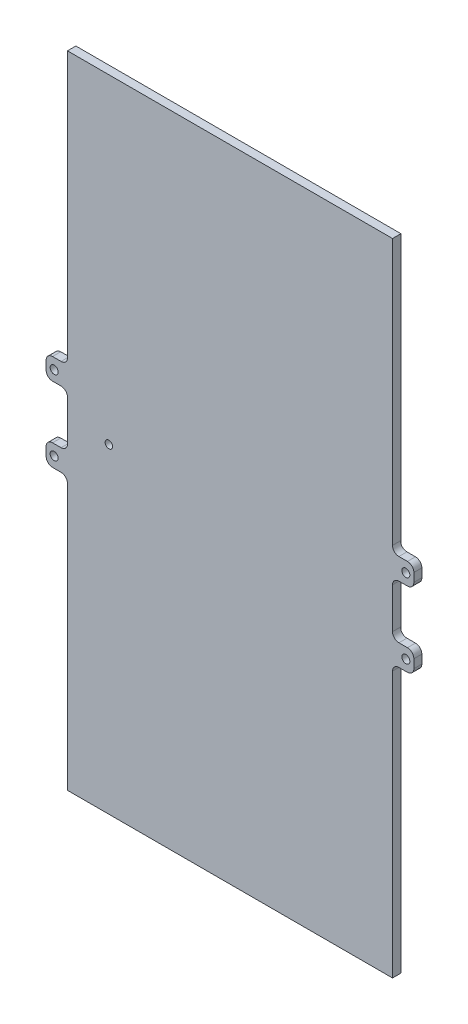
SolidWorks part; units mm, degrees
ref_plane "Front Plane" through (0, 0, 0) normal (1, 0, 0) x (0, 1, 0)
ref_plane "Top Plane" through (0, 0, 0) normal (0, 0, 1) x (0, 1, 0)
ref_plane "Right Plane" through (0, 0, 0) normal (0, 1, 0) x (-1, 0, 0)
sketch "Sketch1" plane through (0, 0, 0) normal (0, 0, 1) x (0, 1, 0)
  line L1 (-60, -30.45) -> (60, -30.45)
  line L2 (-60, -30.45) -> (-60, 30.45)
  line L3 (-60, 30.45) -> (60, 30.45)
  line L4 (60, -30.45) -> (60, 30.45)
  line L5 (-60, -30.45) -> (60, 30.45) construction
  line L6 (-60, 30.45) -> (60, -30.45) construction
  point P0 (0, 0)
  dimension "D1" = 120
  dimension "D2" = 60.9
extrude "Boss-Extrude1" add sketch "Sketch1" along normal blind 1.61
sketch "Sketch2" plane through (0, 0, 0) normal (0, 0, -1) x (1, 0, 0)
  line L1 (28.4817, 0) -> (17.4151, 6.3893)
  line L2 (17.4151, 6.3893) -> (17.4151, -6.3893)
  line L3 (17.4151, -6.3893) -> (28.4817, 0)
  circle A0 centre (21.104, 0) radius 3.6889 construction
extrude "Cut-Extrude1" cut sketch "Sketch2" against normal blind 0.5 contours L3 L1 L2
sketch "Sketch3" plane through (-30.45, 0, 0) normal (-1, 0, 0) x (0, -1, 0)
  line L0 (-60, 1.61) -> (-60, 0) construction
  line L1 (60, 0.035) -> (-60, 0.035)
  line L2 (60, 0.035) -> (60, 1.575)
  line L3 (60, 1.575) -> (-60, 1.575)
  line L4 (-60, 0.035) -> (-60, 1.575)
  line L5 (60, 0.035) -> (-60, 1.575) construction
  line L6 (60, 1.575) -> (-60, 0.035) construction
  line L7 (-60, 1.61) -> (60, 1.61) construction
  line L8 (-60, 0) -> (60, 0) construction
  line L9 (-9, 0.035) -> (-5, 0.035)
  line L10 (-9, 0.035) -> (-9, 1.575)
  line L11 (-9, 1.575) -> (-5, 1.575)
  line L12 (-5, 0.035) -> (-5, 1.575)
  line L13 (-9, 0.035) -> (-5, 1.575) construction
  line L14 (-9, 1.575) -> (-5, 0.035) construction
  line L15 (5, 0.035) -> (9, 0.035)
  line L16 (5, 0.035) -> (5, 1.575)
  line L17 (5, 1.575) -> (9, 1.575)
  line L18 (9, 0.035) -> (9, 1.575)
  line L19 (5, 0.035) -> (9, 1.575) construction
  line L20 (5, 1.575) -> (9, 0.035) construction
  point P0 (0, 0.805)
  point P9 (-7, 0.805)
  point P14 (7, 0.805)
  dimension "D1" = 0.035
  dimension "D2" = 0.035
  dimension "D3" = 4
  dimension "D4" = 4
  dimension "D5" = 5
  dimension "D6" = 5
sketch "Sketch5" plane through (30.45, 0, 0) normal (1, 0, 0) x (0, 1, 0)
  line L0 (-60, 0.035) -> (-60, 1.575) construction
  line L1 (60, 1.54) -> (-60, 1.54)
  line L2 (60, 1.54) -> (60, 0.07)
  line L3 (60, 0.07) -> (-60, 0.07)
  line L4 (-60, 1.54) -> (-60, 0.07)
  line L5 (60, 1.54) -> (-60, 0.07) construction
  line L6 (60, 0.07) -> (-60, 1.54) construction
  line L7 (-60, 0.035) -> (60, 0.035) construction
  line L9 (9, 0.07) -> (5, 0.07)
  line L10 (9, 0.07) -> (9, 1.54)
  line L11 (9, 1.54) -> (5, 1.54)
  line L12 (5, 0.07) -> (5, 1.54)
  line L13 (9, 0.07) -> (5, 1.54) construction
  line L14 (9, 1.54) -> (5, 0.07) construction
  line L15 (-9, 0.07) -> (-5, 0.07)
  line L16 (-9, 0.07) -> (-9, 1.54)
  line L17 (-9, 1.54) -> (-5, 1.54)
  line L18 (-5, 0.07) -> (-5, 1.54)
  line L19 (-9, 0.07) -> (-5, 1.54) construction
  line L20 (-9, 1.54) -> (-5, 0.07) construction
  point P0 (0, 0.805)
  point P10 (7, 0.805)
  point P15 (-7, 0.805)
  dimension "D1" = 0.035
  dimension "D2" = 4
  dimension "D3" = 4
  dimension "D4" = 5
  dimension "D5" = 5
extrude "Boss-Extrude2" add sketch "Sketch3" along normal blind 4 contours L10 L11 L12 L9 | L18 L17 L16 L15
extrude "Boss-Extrude3" add sketch "Sketch5" along normal blind 4 contours L12 L11 L10 L9 | L18 L17 L16 L15
sketch "Sketch7" plane through (0, 0, 1.54) normal (0, 0, 1) x (1, 0, 0)
  line L0 (-34.45, 9) -> (-30.45, 9) construction
  line L1 (-34.45, 9) -> (-34.45, 5) construction
  line L2 (-34.45, -9) -> (-30.45, -9) construction
  line L3 (-34.45, -5) -> (-34.45, -9) construction
  line L4 (34.45, -9) -> (30.45, -9) construction
  line L5 (34.45, -9) -> (34.45, -5) construction
  line L6 (34.45, 9) -> (30.45, 9) construction
  line L7 (34.45, 9) -> (34.45, 5) construction
  circle A0 centre (32.95, 7) radius 0.75
  circle A1 centre (32.95, -7) radius 0.75
  circle A2 centre (-32.95, -7) radius 0.75
  circle A3 centre (-32.95, 7) radius 0.75
  dimension "D1" = 1.5
  dimension "D2" = 1.5
  dimension "D3" = 1.5
  dimension "D4" = 1.5
  dimension "D8" = 1.5
  dimension "D9" = 2
  dimension "D10" = 1.5
  dimension "D11" = 2
  dimension "D12" = 1.5
  dimension "D5" = 2
  dimension "D6" = 1.5
  dimension "D7" = 2
extrude "Cut-Extrude3" cut sketch "Sketch7" against normal through all both and the other way through all contours A0 | A1 | A2 | A3
fillet "Fillet1" radius 1.2 8 edges at (30.45, 9, 0.805) (30.45, -5, 0.805) (30.45, -9, 0.805) (30.45, 5, 0.805) (-30.45, 9, 0.805) (-30.45, 5, 0.805) (-30.45, -9, 0.805) (-30.45, -5, 0.805)
fillet "Fillet2" radius 1.2 8 edges at (-34.45, -9, 0.805) (-34.45, -5, 0.805) (-34.45, 5, 0.805) (-34.45, 9, 0.805) (34.45, 9, 0.805) (34.45, 5, 0.805) (34.45, -9, 0.805) (34.45, -5, 0.805)
sketch "Sketch8" plane through (0, 0, 0) normal (0, 0, -1) x (1, 0, 0)
  line L0 (-30.45, -60) -> (-30.45, 60) construction
  circle A0 centre (-22.7, 0) radius 0.7
  dimension "D2" = 1.4
  dimension "D1" = 7.75
extrude "Cut-Extrude4" cut sketch "Sketch8" against normal through all contours A0
sketch "Sketch9" plane through (0, 0, 0.07) normal (0, 0, -1) x (-1, 0, 0)
  line L0 (-30.45, -10.2) -> (-30.45, -3.8) construction
  point P0 (-30.45, -7)
sketch "Sketch13" plane through (0, 0, 1.61) normal (0, 0, 1) x (1, 0, 0)
  line L1 (-30.45, 60) -> (30.45, 60)
  line L2 (-30.45, 60) -> (-30.45, -60)
  line L3 (-30.45, -60) -> (30.45, -60)
  line L4 (30.45, 60) -> (30.45, -60)
extrude "Cut-Extrude5" cut sketch "Sketch13" against normal blind 0.04
sketch "Sketch14" plane through (0, 0, 1.54) normal (0, 0, 1) x (1, 0, 0)
  line L0 (31.65, -9) -> (33.25, -9) construction
  line L1 (34.45, -7.8) -> (34.45, -6.2) construction
  line L2 (33.25, -5) -> (31.65, -5) construction
  line L3 (30.45, -3.8) -> (30.45, -10.2) construction
  line L4 (34.45, 6.2) -> (34.45, 7.8) construction
  line L5 (33.25, 9) -> (31.65, 9) construction
  line L6 (30.45, 10.2) -> (30.45, 3.8) construction
  line L7 (31.65, 5) -> (33.25, 5) construction
  line L8 (31.65, -9) -> (33.25, -9)
  line L9 (34.45, -7.8) -> (34.45, -6.2)
  line L10 (33.25, -5) -> (31.65, -5)
  line L11 (30.45, -3.8) -> (30.45, -10.2)
  line L12 (34.45, 6.2) -> (34.45, 7.8)
  line L13 (33.25, 9) -> (31.65, 9)
  line L14 (30.45, 10.2) -> (30.45, 3.8)
  line L15 (31.65, 5) -> (33.25, 5)
  arc A0 (33.25, -9) -> (34.45, -7.8) centre (33.25, -7.8) ccw construction
  arc A1 (34.45, -6.2) -> (33.25, -5) centre (33.25, -6.2) ccw construction
  arc A2 (30.45, -3.8) -> (31.65, -5) centre (31.65, -3.8) ccw construction
  arc A3 (31.65, -9) -> (30.45, -10.2) centre (31.65, -10.2) ccw construction
  arc A4 (34.45, 7.8) -> (33.25, 9) centre (33.25, 7.8) ccw construction
  arc A5 (30.45, 10.2) -> (31.65, 9) centre (31.65, 10.2) ccw construction
  arc A6 (31.65, 5) -> (30.45, 3.8) centre (31.65, 3.8) ccw construction
  arc A7 (33.25, 5) -> (34.45, 6.2) centre (33.25, 6.2) ccw construction
  arc A8 (33.25, -9) -> (34.45, -7.8) centre (33.25, -7.8) ccw
  arc A9 (34.45, -6.2) -> (33.25, -5) centre (33.25, -6.2) ccw
  arc A10 (30.45, -3.8) -> (31.65, -5) centre (31.65, -3.8) ccw
  arc A11 (31.65, -9) -> (30.45, -10.2) centre (31.65, -10.2) ccw
  arc A12 (34.45, 7.8) -> (33.25, 9) centre (33.25, 7.8) ccw
  arc A13 (30.45, 10.2) -> (31.65, 9) centre (31.65, 10.2) ccw
  arc A14 (31.65, 5) -> (30.45, 3.8) centre (31.65, 3.8) ccw
  arc A15 (33.25, 5) -> (34.45, 6.2) centre (33.25, 6.2) ccw
  circle A16 centre (32.95, -7) radius 0.75 construction
  circle A17 centre (32.95, 7) radius 0.75 construction
  circle A18 centre (32.95, -7) radius 0.75
  circle A19 centre (32.95, 7) radius 0.75
extrude "Boss-Extrude4" add sketch "Sketch14" along normal blind 0.03
sketch "Sketch15" plane through (0, 0, 1.575) normal (0, 0, 1) x (1, 0, 0)
  line L0 (-34.45, 7.8) -> (-34.45, 6.2) construction
  line L1 (-33.25, 5) -> (-31.65, 5) construction
  line L2 (-30.45, 3.8) -> (-30.45, 10.2) construction
  line L3 (-31.65, 9) -> (-33.25, 9) construction
  line L4 (-34.45, -6.2) -> (-34.45, -7.8) construction
  line L5 (-33.25, -9) -> (-31.65, -9) construction
  line L6 (-30.45, -10.2) -> (-30.45, -3.8) construction
  line L7 (-31.65, -5) -> (-33.25, -5) construction
  line L8 (-34.45, 7.8) -> (-34.45, 6.2)
  line L9 (-33.25, 5) -> (-31.65, 5)
  line L10 (-30.45, 3.8) -> (-30.45, 10.2)
  line L11 (-31.65, 9) -> (-33.25, 9)
  line L12 (-34.45, -6.2) -> (-34.45, -7.8)
  line L13 (-33.25, -9) -> (-31.65, -9)
  line L14 (-30.45, -10.2) -> (-30.45, -3.8)
  line L15 (-31.65, -5) -> (-33.25, -5)
  arc A0 (-34.45, 6.2) -> (-33.25, 5) centre (-33.25, 6.2) ccw construction
  arc A1 (-30.45, 3.8) -> (-31.65, 5) centre (-31.65, 3.8) ccw construction
  arc A2 (-31.65, 9) -> (-30.45, 10.2) centre (-31.65, 10.2) ccw construction
  arc A3 (-33.25, 9) -> (-34.45, 7.8) centre (-33.25, 7.8) ccw construction
  arc A4 (-34.45, -7.8) -> (-33.25, -9) centre (-33.25, -7.8) ccw construction
  arc A5 (-30.45, -10.2) -> (-31.65, -9) centre (-31.65, -10.2) ccw construction
  arc A6 (-31.65, -5) -> (-30.45, -3.8) centre (-31.65, -3.8) ccw construction
  arc A7 (-33.25, -5) -> (-34.45, -6.2) centre (-33.25, -6.2) ccw construction
  arc A8 (-34.45, 6.2) -> (-33.25, 5) centre (-33.25, 6.2) ccw
  arc A9 (-30.45, 3.8) -> (-31.65, 5) centre (-31.65, 3.8) ccw
  arc A10 (-31.65, 9) -> (-30.45, 10.2) centre (-31.65, 10.2) ccw
  arc A11 (-33.25, 9) -> (-34.45, 7.8) centre (-33.25, 7.8) ccw
  arc A12 (-34.45, -7.8) -> (-33.25, -9) centre (-33.25, -7.8) ccw
  arc A13 (-30.45, -10.2) -> (-31.65, -9) centre (-31.65, -10.2) ccw
  arc A14 (-31.65, -5) -> (-30.45, -3.8) centre (-31.65, -3.8) ccw
  arc A15 (-33.25, -5) -> (-34.45, -6.2) centre (-33.25, -6.2) ccw
  circle A16 centre (-32.95, -7) radius 0.75 construction
  circle A17 centre (-32.95, 7) radius 0.75 construction
  circle A18 centre (-32.95, -7) radius 0.75
  circle A19 centre (-32.95, 7) radius 0.75
extrude "Cut-Extrude6" cut sketch "Sketch15" against normal up to surface (0.005 mm away) up to face at (16.5583, 0, 1.57)
